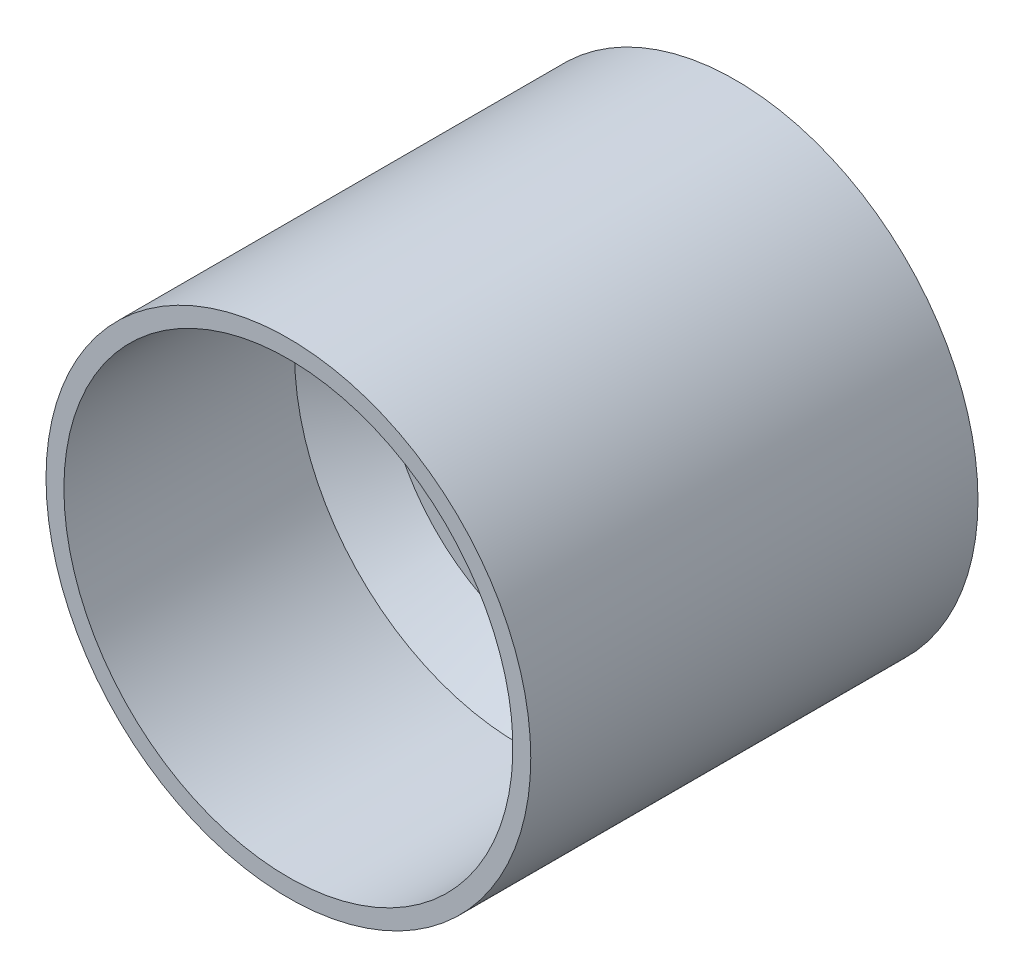
SolidWorks part; units mm, degrees
material "ABS"
ref_plane "Front Plane" through (0, 0, 0) normal (0, 0, 1) x (1, 0, 0)
ref_plane "Top Plane" through (0, 0, 0) normal (0, 1, 0) x (1, 0, 0)
ref_plane "Right Plane" through (0, 0, 0) normal (1, 0, 0) x (0, 0, -1)
sketch "Sketch1" plane through (0, 0, 0) normal (0, 1, 0) x (1, 0, 0)
  line L0 (0, 51.2882) -> (0, -69.4276) construction
  line L1 (15.25, 26.5) -> (15.25, 23.5)
  line L2 (15.25, 23.5) -> (25.1, 23.5)
  line L3 (25.1, 23.5) -> (25.1, -23.5)
  line L4 (25.1, -23.5) -> (27.1, -23.5)
  line L5 (27.1, -23.5) -> (27.1, 26.5)
  line L6 (27.1, 26.5) -> (15.25, 26.5)
  point P9 (25.1, 0)
  dimension "D1" = 30.5
  dimension "D2" = 3
  dimension "D3" = 2
  dimension "D4" = 50.2
  dimension "D6" = 50
revolve "Revolve1" add sketch "Sketch1" angle 360 about L0
sketch "Sketch2" plane through (0, 0, -26.5) normal (0, 0, -1) x (-1, 0, 0)
  circle A0 centre (0, 0) radius 20.25 construction
  circle A1 centre (0, 20.25) radius 2
  circle A2 centre (17.537, -10.125) radius 2
  circle A3 centre (-17.537, -10.125) radius 2
  point P12 (0, 0)
  dimension "D1" = 40.5
  dimension "D2" = 4
  dimension "D3" = 3
extrude "Cut-Extrude1" cut sketch "Sketch2" against normal blind 10
sketch "Sketch3" plane through (0, 0, 0) normal (0, 1, 0) x (1, 0, 0)
  line L0 (25.1, 10.3) -> (0, 10.3)
  line L1 (25.1, 23.5) -> (25.1, -23.5) construction
  line L2 (27.1, 26.5) -> (15.25, 26.5) construction
  line L3 (0, 10.3) -> (0, 7.3)
  line L4 (0, 7.3) -> (25.1, 7.3)
  line L5 (25.1, 7.3) -> (25.1, 10.3)
  line L6 (0, 51.2882) -> (0, -69.4276) construction
  dimension "D1" = 3
  dimension "D2" = 16.2
revolve "Revolve2" add sketch "Sketch3" angle 360 about L0
chamfer "Chamfer1" distance 5 angle 45 2 edges at (-25.1, 0, -7.3) (25.1, 0, -10.3)
sketch "Sketch4" plane through (0, 0, -10.3) normal (0, 0, -1) x (-1, 0, 0)
  line L0 (-6.05, 3.6194) -> (-6.05, -3.6194)
  line L1 (6.05, -3.6194) -> (6.05, 3.6194)
  line L2 (0, 15.25) -> (0, -15.25) construction
  line L3 (0, 0) -> (0, -84.6003) construction
  line L4 (-25.1, 0) -> (-27.1, 0) construction
  line L5 (-6.364, 6.364) -> (6.364, 6.364) construction
  circle A0 centre (0, 0) radius 9 construction
  arc A1 (-6.05, -3.6194) -> (6.05, -3.6194) centre (0, 0) ccw
  arc A2 (6.05, 3.6194) -> (-6.05, 3.6194) centre (0, 0) ccw
  circle A3 centre (-6.364, 6.364) radius 1.1
  circle A4 centre (6.364, 6.364) radius 1.1
  circle A5 centre (6.364, -6.364) radius 1.1
  circle A6 centre (-6.364, -6.364) radius 1.1
  circle A7 centre (0, 0) radius 15.25 construction
  circle A8 centre (0, 12.5) radius 1.5
  circle A9 centre (0, -12.5) radius 1.5
  circle A10 centre (0, 0) radius 11 construction
  point P21 (0, 0)
  dimension "D1" = 18
  dimension "D2" = 14.1
  dimension "D5" = 2.2
  dimension "D7" = 3
  dimension "D8" = 3
  dimension "D12" = 22
  dimension "D3" = 12.1
  dimension "D4" = 12.1
  dimension "D9" = 12.5
  dimension "D10" = 12.5
  dimension "D11" = 0
  dimension "D6" = 4
extrude "Cut-Extrude2" cut sketch "Sketch4" against normal blind 10
